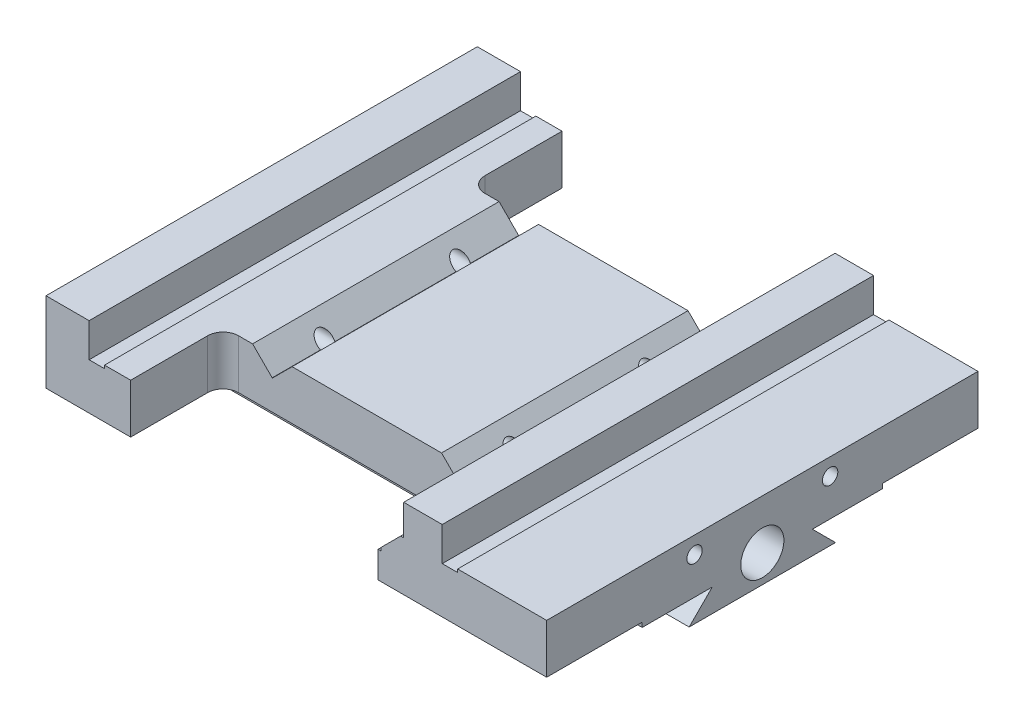
SolidWorks part; units mm, degrees
ref_plane "Front Plane" through (0, 0, 0) normal (0, 0, 1) x (1, 0, 0)
ref_plane "Top Plane" through (0, 0, 0) normal (0, 1, 0) x (1, 0, 0)
ref_plane "Right Plane" through (0, 0, 0) normal (1, 0, 0) x (0, 0, -1)
sketch "Sketch1" plane through (0, 0, 0) normal (0, 0, 1) x (1, 0, 0)
  line L1 (-148.8234, 16.364) -> (-134.8234, 16.364)
  line L2 (-134.8234, 16.364) -> (-134.8234, 6.364)
  line L3 (-129.8234, 6.364) -> (-111.7719, 6.364)
  line L4 (-111.7719, 6.364) -> (-105.4079, 0)
  line L5 (-105.4079, 0) -> (-105.3079, 0)
  line L6 (-105.3079, 0) -> (-98.944, 6.364)
  line L7 (-98.944, 6.364) -> (-50.444, 6.364)
  line L8 (-50.444, 6.364) -> (-44.08, 0)
  line L10 (-40.08, 0) -> (-33.7161, 6.364)
  line L11 (-33.7161, 6.364) -> (-32.7161, 6.364)
  line L12 (-32.7161, 6.364) -> (-32.7161, 16.364)
  line L13 (-32.7161, 16.364) -> (-20.2161, 16.364)
  line L15 (-15.2161, 6.364) -> (13.6766, 6.364)
  line L16 (13.6766, 6.364) -> (13.6766, -9.636)
  line L17 (13.6766, -9.636) -> (-148.8234, -9.636)
  line L19 (-134.8234, 6.364) -> (-134.8234, 5.364)
  line L20 (-134.8234, 5.364) -> (-129.8234, 5.364)
  line L21 (-129.8234, 5.364) -> (-129.8234, 6.364)
  line L22 (-40.08, 0) -> (-40.08, -1)
  line L23 (-40.08, -1) -> (-44.08, -1)
  line L24 (-44.08, -1) -> (-44.08, 0)
  line L25 (-15.2161, 6.364) -> (-15.2161, 5.364)
  line L26 (-15.2161, 5.364) -> (-20.2161, 5.364)
  line L28 (-20.2161, 5.364) -> (-20.2161, 16.364)
  line L29 (-148.8234, 16.364) -> (-148.8234, -9.636)
  dimension "D1" = 162.5
  dimension "D2" = 9
  dimension "D3" = 9
  dimension "D4" = 0.1
  dimension "D5" = 9
  dimension "D6" = 9
  dimension "D7" = 4
  dimension "D8" = 12.5
  dimension "D9" = 48.5
  dimension "D10" = 1
  dimension "D11" = 14
  dimension "D12" = 225
  dimension "D13" = 16
  dimension "D15" = 90
  dimension "D16" = 1
  dimension "D17" = 5
  dimension "D18" = 1
  dimension "D19" = 1
  dimension "D21" = 5
  dimension "D22" = 1
  dimension "D24" = 26
  dimension "D25" = 1
extrude "Boss-Extrude1" add sketch "Sketch1" along normal blind 140
sketch "Sketch2" plane through (13.6766, 0, 0) normal (1, 0, 0) x (0, 0, -1)
  line L0 (-86.25, -11.136) -> (-93.75, -18.636)
  line L1 (-140, -9.636) -> (0, -9.636) construction
  line L2 (-93.75, -18.636) -> (-46.25, -18.636)
  line L3 (-46.25, -18.636) -> (-53.75, -11.136)
  line L5 (-53.75, -11.136) -> (-31, -11.136)
  line L6 (-31, -11.136) -> (-31, -8.7131)
  line L7 (-31, -8.7131) -> (-109, -8.7131)
  line L8 (-109, -8.7131) -> (-109, -11.136)
  line L9 (-109, -11.136) -> (-86.25, -11.136)
  line L10 (0, -9.636) -> (0, 6.364) construction
  point P10 (0, 0)
  point P11 (-88.5967, -9.636)
  point P12 (0, 0)
  point P15 (-109, -9.9246)
  dimension "D1" = 45
  dimension "D2" = 45
  dimension "D3" = 1.5
  dimension "D4" = 78
  dimension "D5" = 31
  dimension "D6" = 47.5
  dimension "D7" = 15.25
  dimension "D8" = 7.5
extrude "Boss-Extrude2" add sketch "Sketch2" against normal blind 162.5
sketch "Sketch3" plane through (0, -9.636, 0) normal (0, -1, 0) x (1, 0, 0)
  line L0 (-148.8234, 0) -> (13.6766, 0) construction
  line L1 (-121.3429, 0) -> (-41.0392, 0)
  line L2 (-121.3429, 0) -> (-121.3429, 25)
  line L3 (-116.3429, 30) -> (-46.0392, 30)
  line L4 (-41.0392, 0) -> (-41.0392, 25)
  line L5 (-148.8234, 140) -> (13.6766, 140) construction
  line L6 (-121.3429, 140) -> (-41.0392, 140)
  line L7 (-121.3429, 140) -> (-121.3429, 115)
  line L8 (-116.3429, 110) -> (-46.0392, 110)
  line L9 (-41.0392, 140) -> (-41.0392, 115)
  line L10 (-148.8234, 140) -> (13.6766, 140) construction
  arc A0 (-46.0392, 30) -> (-41.0392, 25) centre (-46.0392, 25) cw
  arc A1 (-121.3429, 25) -> (-116.3429, 30) centre (-116.3429, 25) cw
  arc A2 (-46.0392, 110) -> (-41.0392, 115) centre (-46.0392, 115) ccw
  arc A3 (-121.3429, 115) -> (-116.3429, 110) centre (-116.3429, 115) ccw
  dimension "D1" = 5
  dimension "D2" = 30
  dimension "D3" = 30
extrude "Cut-Extrude1" cut sketch "Sketch3" against normal blind 100
sketch "Sketch4" plane through (13.6766, 0, 0) normal (1, 0, 0) x (0, 0, -1)
  line L0 (-93.75, -18.636) -> (-46.25, -18.636) construction
  line L1 (-140, -9.636) -> (-140, 6.364) construction
  circle A0 centre (-70, -9.636) radius 7
  dimension "D1" = 14
  dimension "D2" = 9
  dimension "D3" = 70
extrude "Cut-Extrude2" cut sketch "Sketch4" against normal blind 1000
sketch "Sketch5" plane through (13.6766, 0, 0) normal (1, 0, 0) x (0, 0, -1)
  line L0 (-140, 6.364) -> (0, 6.364) construction
  circle A0 centre (-92, 0.864) radius 2.5
  circle A2 centre (-48, 0.864) radius 2.5
  circle A3 centre (-70, -9.636) radius 7 construction
  dimension "D2" = 5
  dimension "D3" = 5.5
  dimension "D4" = 44
  dimension "D5" = 22
  dimension "D1" = 2
extrude "Cut-Extrude3" cut sketch "Sketch5" against normal blind 1000
